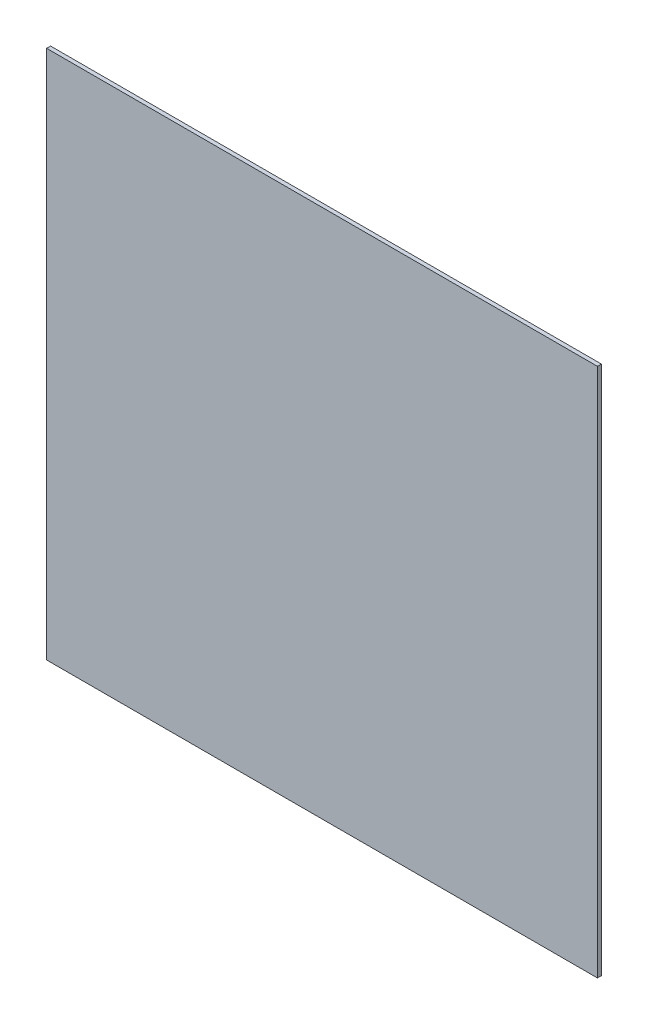
SolidWorks part; units mm, degrees
material "Acrylic (Medium-high impact)"
ref_plane "Front Plane" through (0, 0, 0) normal (0, 0, 1) x (1, 0, 0)
ref_plane "Top Plane" through (0, 0, 0) normal (0, 1, 0) x (1, 0, 0)
ref_plane "Right Plane" through (0, 0, 0) normal (1, 0, 0) x (0, 0, -1)
sketch "Sketch1" plane through (0, 0, 0) normal (0, 0, 1) x (1, 0, 0)
  line L6 (-208.661, 200.66) -> (208.661, 200.66)
  line L14 (-208.661, 200.66) -> (-208.661, -200.66)
  line L15 (-208.661, -200.66) -> (208.661, -200.66)
  line L17 (-208.661, 200.66) -> (208.661, -200.66) construction
  line L18 (-208.661, -200.66) -> (208.661, 200.66) construction
  line L22 (208.661, 200.66) -> (208.661, -200.66)
  point P0 (0, 0)
  dimension "D1" = 401.32
  dimension "D2" = 417.322
extrude "Boss-Extrude1" add sketch "Sketch1" along normal blind 2.9972
